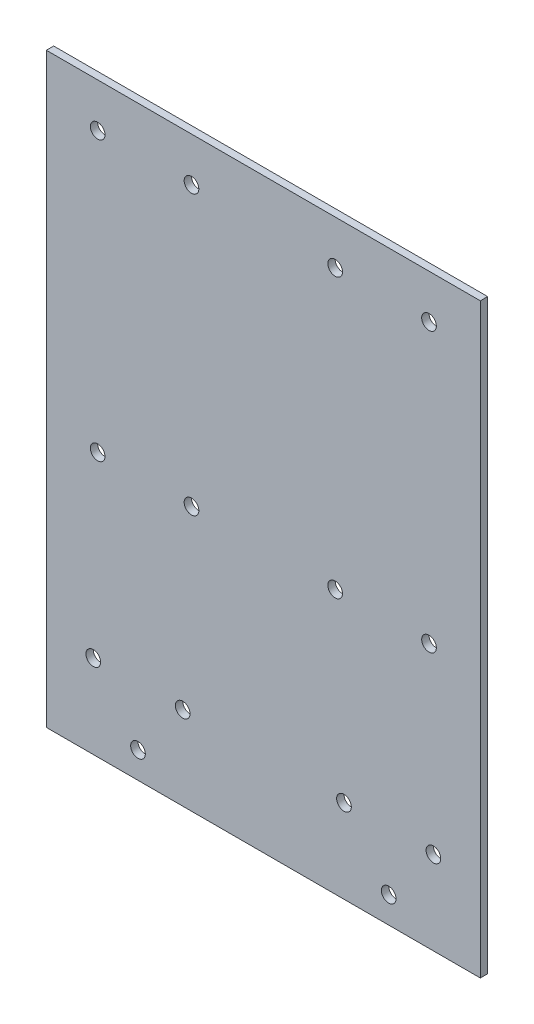
SolidWorks part; units mm, degrees
ref_plane "前视基准面" through (0, 0, 0) normal (0, 0, 1) x (1, 0, 0)
ref_plane "上视基准面" through (0, 0, 0) normal (0, 1, 0) x (1, 0, 0)
ref_plane "右视基准面" through (0, 0, 0) normal (1, 0, 0) x (0, 0, -1)
sketch "草图1" plane through (0, 0, 0) normal (0, 0, 1) x (1, 0, 0)
  line L0 (0, -100) -> (0, 100) construction
  line L1 (74, -100) -> (-74, -100)
  line L2 (74, -100) -> (74, 100)
  line L3 (74, 100) -> (-74, 100)
  line L4 (-74, -100) -> (-74, 100)
  line L5 (74, -100) -> (-74, 100) construction
  line L6 (74, 100) -> (-74, -100) construction
  circle A0 centre (-58, -71.5) radius 2.5
  circle A1 centre (-27.5, -71.5) radius 2.5
  circle A2 centre (-42.75, -91) radius 2.5
  circle A3 centre (42.75, -91) radius 2.5
  circle A4 centre (58, -71.5) radius 2.5
  circle A5 centre (27.5, -71.5) radius 2.5
  point P0 (0, 0)
  dimension "D3" = 5
  dimension "D4" = 5
  dimension "D5" = 5
  dimension "D6" = 9
  dimension "D7" = 16
  dimension "D8" = 30.5
  dimension "D9" = 19.5
  dimension "D10" = 15.25
  dimension "D1" = 148
  dimension "D2" = 200
extrude "凸台-拉伸1" add sketch "草图1" along normal blind 2.5
sketch "草图2" plane through (0, 0, 2.5) normal (0, 0, 1) x (1, 0, 0)
  line L0 (-74, 100) -> (-74, -100) construction
  line L1 (-74, -100) -> (74, -100) construction
  line L2 (0, 100) -> (0, -100) construction
  line L3 (74, 100) -> (-74, 100) construction
  circle A0 centre (-56.5, -10) radius 2.5
  circle A1 centre (-24.5, -10) radius 2.5
  circle A2 centre (-56.5, 85) radius 2.5
  circle A3 centre (-24.5, 85) radius 2.5
  circle A8 centre (24.5, 85) radius 2.5
  circle A9 centre (56.5, 85) radius 2.5
  circle A10 centre (24.5, -10) radius 2.5
  circle A11 centre (56.5, -10) radius 2.5
  circle A12 centre (-56.5, 180) radius 2.5 [skipped]
  circle A13 centre (-24.5, 180) radius 2.5 [skipped]
  dimension "D1" = 5
  dimension "D2" = 5
  dimension "D3" = 32
  dimension "D4" = 17.5
  dimension "D5" = 90
  dimension "D7" = 90
  dimension "D6" = 3
extrude "切除-拉伸1" cut sketch "草图2" against normal blind 3
